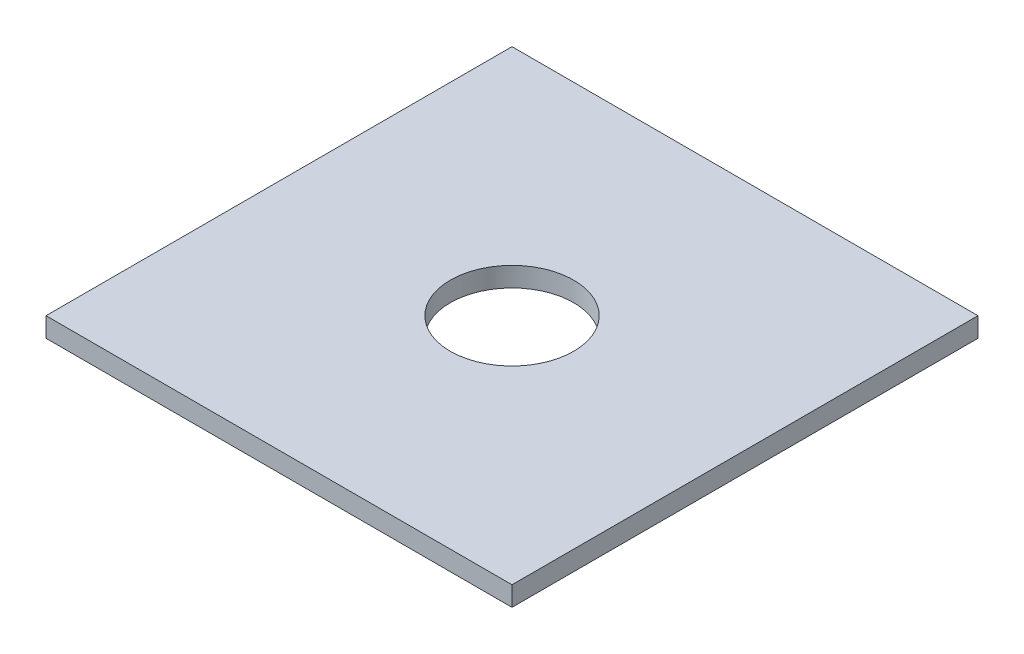
SolidWorks part; units mm, degrees
ref_plane "Front Plane" through (0, 0, 0) normal (0, 0, 1) x (1, 0, 0)
ref_plane "Top Plane" through (0, 0, 0) normal (0, 1, 0) x (1, 0, 0)
ref_plane "Right Plane" through (0, 0, 0) normal (1, 0, 0) x (0, 0, -1)
sketch "Sketch1" plane through (0, 0, 0) normal (0, 1, 0) x (1, 0, 0)
  line L1 (-119, -119) -> (119, -119)
  line L2 (-119, -119) -> (-119, 119)
  line L3 (-119, 119) -> (119, 119)
  line L4 (119, -119) -> (119, 119)
  line L5 (-119, -119) -> (119, 119) construction
  line L6 (-119, 119) -> (119, -119) construction
  circle A0 centre (0, 0) radius 31.5
  point P0 (0, 0)
  dimension "D3" = 63
  dimension "D1" = 238
  dimension "D2" = 238
extrude "Boss-Extrude1" add sketch "Sketch1" along normal blind 10
